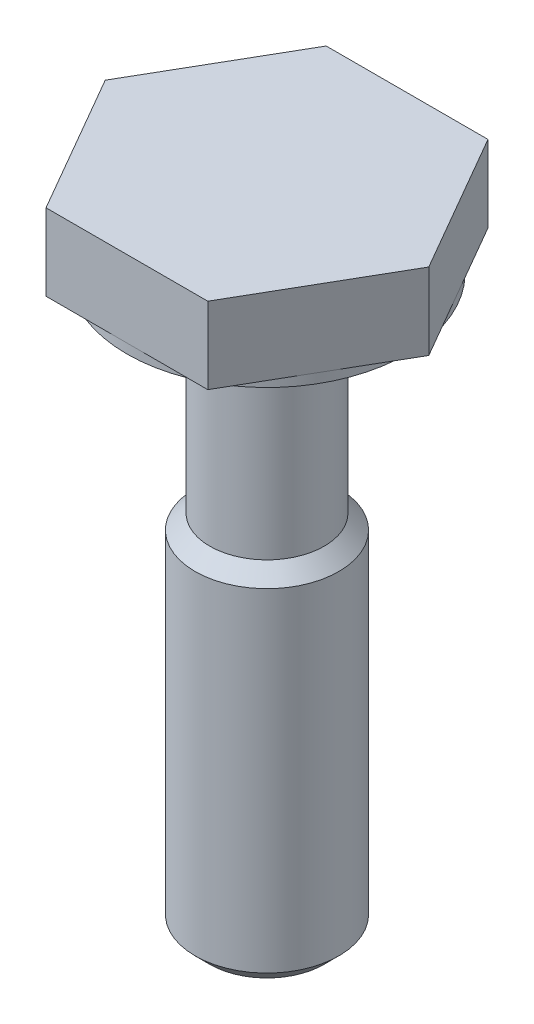
SolidWorks part; units mm, degrees
material "Хромистая нержавеющая сталь"
ref_plane "Спереди" through (0, 0, 0) normal (0, 0, 1) x (1, 0, 0)
ref_plane "Сверху" through (0, 0, 0) normal (0, 1, 0) x (1, 0, 0)
ref_plane "Справа" through (0, 0, 0) normal (1, 0, 0) x (0, 0, -1)
sketch "Эскиз1" plane through (0, 0, 0) normal (0, 0, 1) x (1, 0, 0)
  line L0 (0, 0) -> (0, -10.95) construction
  line L1 (-2.875, 1.8) -> (0, 1.8)
  line L2 (-2.875, 1.8) -> (-2.925, 1.75)
  line L3 (-2.925, 1.75) -> (-2.925, 0)
  line L4 (-2.925, 0) -> (-2.5, 0)
  line L5 (-2.5, 0) -> (-2.5, 1)
  line L6 (-2.5, 1) -> (-1.195, 1)
  line L7 (-1.195, 1) -> (-1.195, -4.34)
  line L8 (-1.195, -4.34) -> (-1.5, -4.645)
  line L9 (-1.5, -4.645) -> (-1.5, -11.595)
  line L10 (-1.5, -11.595) -> (-1.195, -11.9)
  line L11 (-1.195, -11.9) -> (-0.65, -11.9)
  line L12 (-0.65, -11.9) -> (0, -11.24)
  line L13 (0, 1.8) -> (0, -11.24)
  dimension "D1" = 5.85
  dimension "D2" = 1.8
  dimension "D3" = 0.05
  dimension "D4" = 45
  dimension "D5" = 2.39
  dimension "D6" = 5
  dimension "D7" = 1
  dimension "D8" = 3
  dimension "D9" = 45
  dimension "D10" = 13.7
  dimension "D11" = 7.56
  dimension "D12" = 0.66
  dimension "D13" = 1.3
revolve "Повернуть1" add sketch "Эскиз1" angle 360 about L0
sketch "Sketch1" plane through (0, 1.8, 0) normal (0, 1, 0) x (1, 0, 0)
  line L1 (1.6887, 2.925) -> (-1.6887, 2.925)
  line L2 (-1.6887, 2.925) -> (-3.3775, 0)
  line L3 (-3.3775, 0) -> (-1.6887, -2.925)
  line L4 (-1.6887, -2.925) -> (1.6887, -2.925)
  line L5 (1.6887, -2.925) -> (3.3775, 0)
  line L6 (3.3775, 0) -> (1.6887, 2.925)
  circle A0 centre (0, 0) radius 2.925 construction
  circle A1 centre (0, 0) radius 2.925 construction
extrude "Boss-Extrude1" add sketch "Sketch1" against normal blind 1.6
